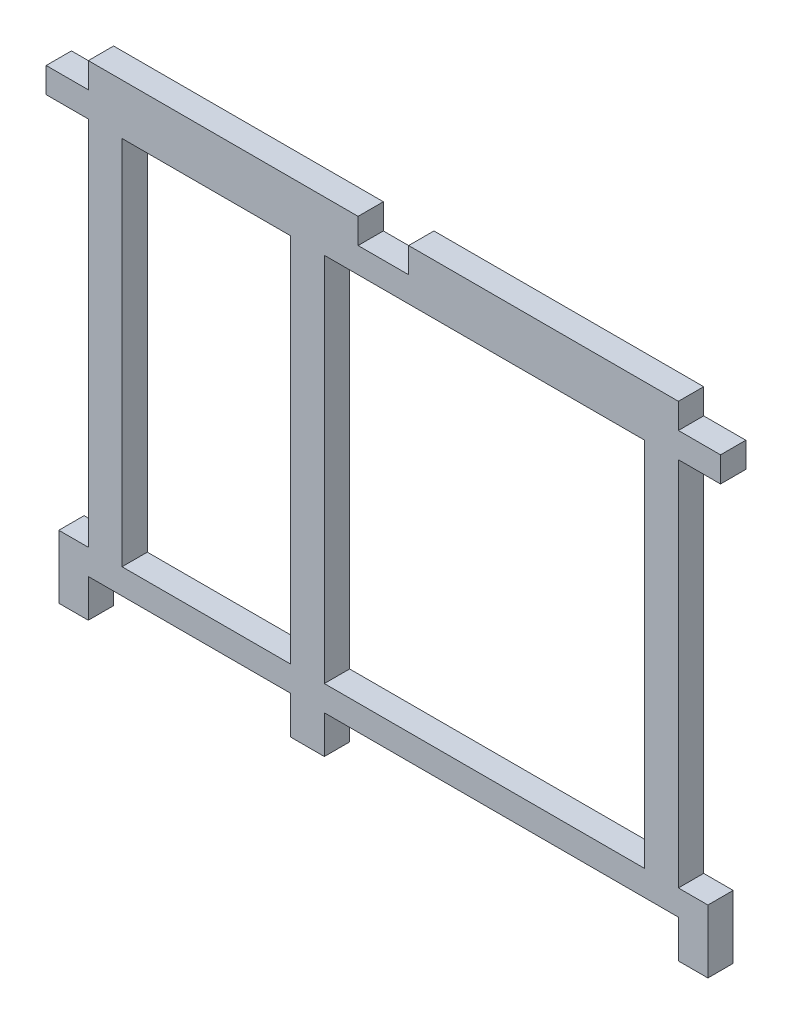
SolidWorks part; units mm, degrees
material "Custom Plastic"
ref_plane "Front Plane" through (0, 0, 0) normal (0, 0, 1) x (1, 0, 0)
ref_plane "Top Plane" through (0, 0, 0) normal (0, 1, 0) x (1, 0, 0)
ref_plane "Right Plane" through (0, 0, 0) normal (1, 0, 0) x (0, 0, -1)
sketch "Sketch1" plane through (0, 0, 0) normal (0, 0, 1) x (1, 0, 0)
  line L75 (5, -3) -> (0, -3)
  line L76 (0, -3) -> (0, 0)
  line L77 (0, 0) -> (5, 0)
  line L78 (5, 0) -> (5, 3)
  line L79 (5, 3) -> (37, 3)
  line L80 (37, 3) -> (37, 0)
  line L81 (37, 0) -> (43, 0)
  line L82 (43, 0) -> (43, 3)
  line L83 (43, 3) -> (75, 3)
  line L84 (75, 3) -> (75, 0)
  line L85 (75, 0) -> (80, 0)
  line L86 (80, 0) -> (80, -3)
  line L87 (80, -3) -> (75, -3)
  line L88 (75, -3) -> (75, -47)
  line L89 (75, -47) -> (78.5, -47)
  line L90 (78.5, -47) -> (78.5, -54.5)
  line L91 (78.5, -54.5) -> (75, -54.5)
  line L92 (75, -54.5) -> (75, -50)
  line L93 (75, -50) -> (33, -50)
  line L94 (33, -50) -> (33, -54.5)
  line L95 (33, -54.5) -> (29, -54.5)
  line L96 (29, -54.5) -> (29, -50)
  line L97 (29, -50) -> (5, -50)
  line L98 (5, -50) -> (5, -54.5)
  line L99 (5, -54.5) -> (1.5, -54.5)
  line L100 (1.5, -54.5) -> (1.5, -47)
  line L101 (1.5, -47) -> (5, -47)
  line L102 (5, -3) -> (5, -47)
  line L103 (9, -47) -> (29, -47)
  line L104 (29, -47) -> (29, -3)
  line L105 (29, -3) -> (9, -3)
  line L106 (9, -3) -> (9, -47)
  line L107 (33, -3) -> (33, -47)
  line L108 (33, -47) -> (71, -47)
  line L109 (71, -47) -> (71, -3)
  line L110 (71, -3) -> (33, -3)
  point P0 (0, 0)
  point P56 (76.75, -47)
  dimension "D4" = 44
  dimension "D13" = 6
  dimension "D14" = 3
  dimension "D15" = 3
  dimension "D16" = 32
  dimension "D17" = 32
  dimension "D18" = 5
  dimension "D19" = 5
  dimension "D20" = 44
  dimension "D21" = 7.5
  dimension "D22" = 3.5
  dimension "D23" = 3
  dimension "D24" = 42
  dimension "D25" = 4
  dimension "D26" = 24
  dimension "D27" = 3.5
  dimension "D28" = 7.5
  dimension "D29" = 4
  dimension "D30" = 4
  dimension "D31" = 20
extrude "Boss-Extrude1" add sketch "Sketch1" along normal blind 3
